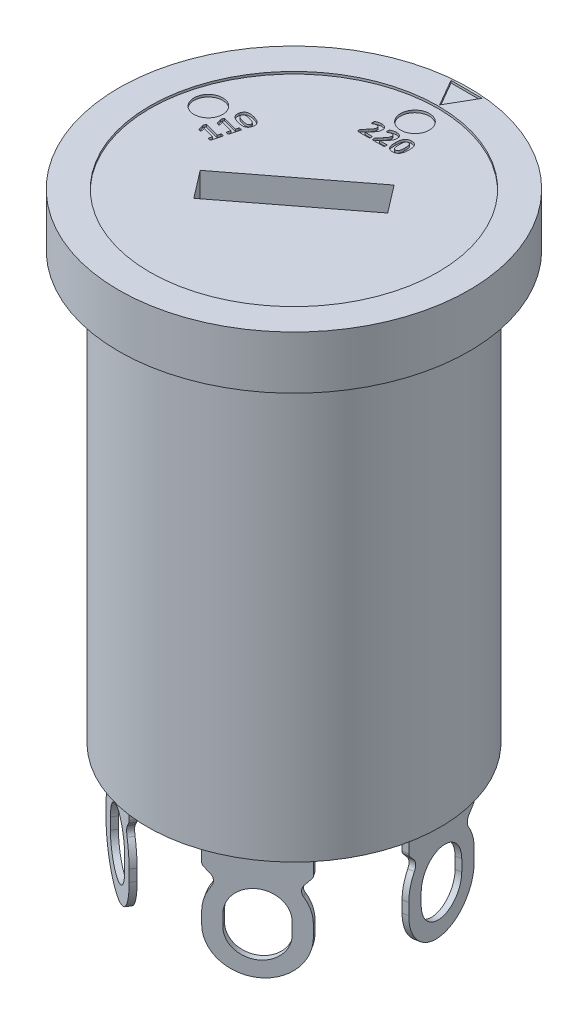
SolidWorks part; units mm, degrees
ref_plane "Front Plane" through (0, 0, 0) normal (0, 0, 1) x (1, 0, 0)
ref_plane "Top Plane" through (0, 0, 0) normal (0, 1, 0) x (1, 0, 0)
ref_plane "Right Plane" through (0, 0, 0) normal (1, 0, 0) x (0, 0, -1)
sketch "Sketch1" plane through (0, 0, 0) normal (0, 1, 0) x (1, 0, 0)
  circle A0 centre (0, 0) radius 7.6
  dimension "D1" = 15.2
extrude "Boss-Extrude1" add sketch "Sketch1" along normal mid plane 2.3
sketch "Sketch2" plane through (0, -1.15, 0) normal (0, -1, 0) x (1, 0, 0)
  circle A0 centre (0, 0) radius 6.35
  dimension "D1" = 12.7
extrude "Boss-Extrude2" add sketch "Sketch2" along normal blind 18.5
sketch "Sketch3" plane through (0, -19.65, 0) normal (0, -1, 0) x (1, 0, 0)
  line L1 (-5.1372, -2.6828) -> (-4.891, -2.6394)
  line L2 (-5.1372, -2.6828) -> (-5.7449, 0.764)
  line L3 (-5.7449, 0.764) -> (-5.4987, 0.8074)
  line L4 (-4.891, -2.6394) -> (-5.4987, 0.8074)
  line L5 (-5.1372, -2.6828) -> (-5.4987, 0.8074) construction
  line L6 (-5.7449, 0.764) -> (-4.891, -2.6394) construction
  line L11 (-5.318, -0.9377) -> (0, 0) construction
  line L12 (0, 0) -> (0, 6.35) construction
  circle A0 centre (0, 0) radius 6.35 construction
  point P0 (-5.318, -0.9377)
  point P27 (0, 0)
  dimension "D1" = 3.5
  dimension "D2" = 0.25
  dimension "D3" = 5.4
  dimension "D4" = 100
extrude "Boss-Extrude3" add sketch "Sketch3" along normal blind 5 contours L3 L4 L1 L2
sketch "Sketch4" plane through (-5.4411, 0, -0.9594) normal (-0.9848, 0, -0.1736) x (-0.1736, 0, 0.9848)
  line L0 (0, -22.4) -> (0, -22.9) construction
  line L1 (1.0847, -22.4) -> (1.0847, -22.9)
  line L2 (-1.0847, -22.4) -> (-1.0847, -22.9)
  line L3 (1.75, -21.2053) -> (0, -19.65) construction
  line L4 (1.75, -24.65) -> (-1.75, -24.65) construction
  line L5 (0, -22.4) -> (1.75, -21.2053) construction
  line L6 (1.75, -24.65) -> (1.75, -19.65) construction
  line L7 (0, -19.65) -> (0, -24.65) construction
  line L9 (1.75, -19.65) -> (-1.75, -19.65) construction
  line L10 (1.4743, -20.9603) -> (1.75, -20.65)
  line L11 (-6.35, -19.65) -> (6.35, -19.65) construction
  line L12 (0, -22.4) -> (-1.75, -21.2053) construction
  line L13 (-1.75, -21.2053) -> (0, -19.65) construction
  line L14 (-1.4743, -20.9603) -> (-1.75, -20.65)
  arc A0 (1.0847, -22.4) -> (-1.0847, -22.4) centre (0, -22.4) ccw
  arc A1 (-1.0847, -22.9) -> (1.0847, -22.9) centre (0, -22.9) ccw
  arc A2 (1.75, -22.4) -> (1.4453, -21.4133) centre (0, -22.4) ccw
  arc A3 (1.75, -22.9) -> (-1.75, -22.9) centre (0, -22.9) cw
  arc A4 (1.4453, -21.4133) -> (1.4743, -20.9603) centre (1.75, -21.2053) cw
  arc A5 (-1.4453, -21.4133) -> (-1.4743, -20.9603) centre (-1.75, -21.2053) ccw
  arc A6 (-1.75, -22.4) -> (-1.4453, -21.4133) centre (0, -22.4) cw
  point P3 (0, -22.65)
  line M8 (-1.75, -19.65) -> (-1.75, -24.65)
  line M9 (-1.75, -24.65) -> (1.75, -24.65)
  line M10 (1.75, -24.65) -> (1.75, -19.65)
  dimension "D3" = 1
  dimension "D1" = 1.75
  dimension "D2" = 0.5
extrude "Cut-Extrude1" cut sketch "Sketch4" against normal up to next (0.25 mm away) contours L2 A1 L1 A0 | A4 A2 L10 M10 | A6 A5 L14 M8 | A3 M9 M8 | A3 M10 M9
fillet "Fillet1" radius 0.2 2 edges at (-5.0141, -20.65, -2.6611) (-5.6218, -20.65, 0.7857)
pattern_circular "CirPattern1" count 4 every 66.667 about axis through (0, 0, 0) along (0, 1, 0) of "Boss-Extrude3", "Cut-Extrude1", "Fillet1"
sketch "Sketch5" plane through (0, 1.15, 0) normal (0, 1, 0) x (1, 0, 0)
  line L1 (0, 6.3206) -> (0.675, 7.4897)
  line L2 (0.675, 7.4897) -> (-0.675, 7.4897)
  line L3 (-0.675, 7.4897) -> (0, 6.3206)
  circle A0 centre (0, 0) radius 6.25
  circle A1 centre (0, 7.1) radius 0.3897 construction
  dimension "D1" = 12.5
  dimension "D2" = 7.1
  dimension "D3" = 1.35
extrude "Cut-Extrude2" cut sketch "Sketch5" against normal blind 0.1
sketch "Sketch6" plane through (0, 1.05, 0) normal (0, 1, 0) x (1, 0, 0)
  line L0 (0, 0) -> (6.25, 0) construction
  line L1 (-2.8366, -1.2313) -> (1.9235, 2.4213)
  line L2 (-2.8366, -1.2313) -> (-1.9235, -2.4213)
  line L3 (-1.9235, -2.4213) -> (2.8366, 1.2313)
  line L4 (1.9235, 2.4213) -> (2.8366, 1.2313)
  line L5 (-2.8366, -1.2313) -> (2.8366, 1.2313) construction
  line L6 (-1.9235, -2.4213) -> (1.9235, 2.4213) construction
  circle A0 centre (0, 0) radius 6.25 construction
  point P0 (0, 0)
  dimension "D1" = 6
  dimension "D2" = 1.5
  dimension "D3" = 37.5
extrude "Cut-Extrude3" cut sketch "Sketch6" against normal blind 3
sketch "Sketch7" plane through (0, 1.05, 0) normal (0, 1, 0) x (1, 0, 0)
  line L0 (-5.0711, 1.3588) -> (0, 0) construction
  line L1 (0, 0) -> (0, 5.25) construction
  line L2 (-1.5, 3.65) -> (1.5, 3.65) construction
  line L3 (-3.1374, 2.3936) -> (-3.9139, -0.5042) construction
  circle A1 centre (0, 5.25) radius 0.625
  circle A2 centre (-5.0711, 1.3588) radius 0.625
  circle A3 centre (0, 0) radius 5.25 construction
  text T0 "110" font "Calibri" height in points 3
  text T1 "220" font "Calibri" height in points 3
  point P13 (0, 3.65)
  point P14 (-3.5256, 0.9447)
  dimension "D1" = 1.25
  dimension "D2" = 1.25
  dimension "D3" = 10.5
  dimension "D4" = 75
  dimension "D5" = 1.6
  dimension "D6" = 3
  dimension "D7" = 3
  dimension "D8" = 1.6
extrude "Cut-Extrude4" cut sketch "Sketch7" against normal blind 0.1
